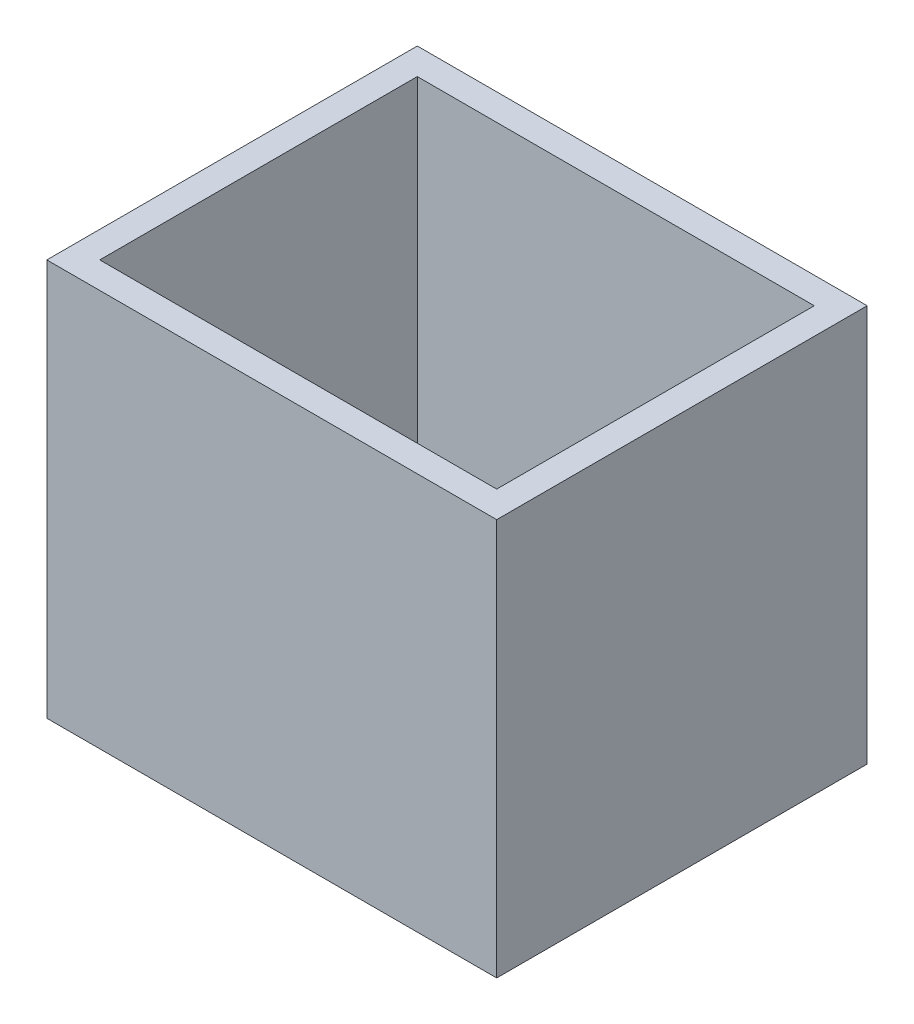
SolidWorks part; units mm, degrees
ref_plane "Front Plane" through (0, 0, 0) normal (0, 0, 1) x (1, 0, 0)
ref_plane "Top Plane" through (0, 0, 0) normal (0, 1, 0) x (1, 0, 0)
ref_plane "Right Plane" through (0, 0, 0) normal (1, 0, 0) x (0, 0, -1)
sketch "Sketch1" plane through (0, 0, 0) normal (0, 1, 0) x (1, 0, 0)
  line L1 (85, 70) -> (0, 70)
  line L2 (85, 70) -> (85, 0)
  line L3 (85, 0) -> (0, 0)
  line L4 (0, 70) -> (0, 0)
  dimension "D1" = 85
  dimension "D2" = 70
extrude "Boss-Extrude1" add sketch "Sketch1" along normal blind 75
sketch "Sketch2" plane through (0, 75, 0) normal (0, 1, 0) x (1, 0, 0)
  line L0 (85, 70) -> (0, 70) construction
  line L1 (5, 65) -> (80, 65)
  line L2 (5, 65) -> (5, 5)
  line L3 (5, 5) -> (80, 5)
  line L4 (80, 65) -> (80, 5)
  line L5 (85, 0) -> (85, 70) construction
  dimension "D1" = 5
  dimension "D2" = 5
  dimension "D3" = 75
  dimension "D4" = 60
extrude "Cut-Extrude1" cut sketch "Sketch2" against normal blind 70
sketch "Sketch3" plane through (0, 5, 0) normal (0, 1, 0) x (1, 0, 0)
  line L0 (80, 5) -> (80, 65) construction
  line L1 (55, 42.4926) -> (75, 42.4926)
  line L2 (55, 42.4926) -> (55, 22.4926)
  line L3 (55, 22.4926) -> (75, 22.4926)
  line L4 (75, 42.4926) -> (75, 22.4926)
  dimension "D1" = 20
  dimension "D2" = 20
  dimension "D3" = 5
extrude "Boss-Extrude2" add sketch "Sketch3" along normal blind 25
